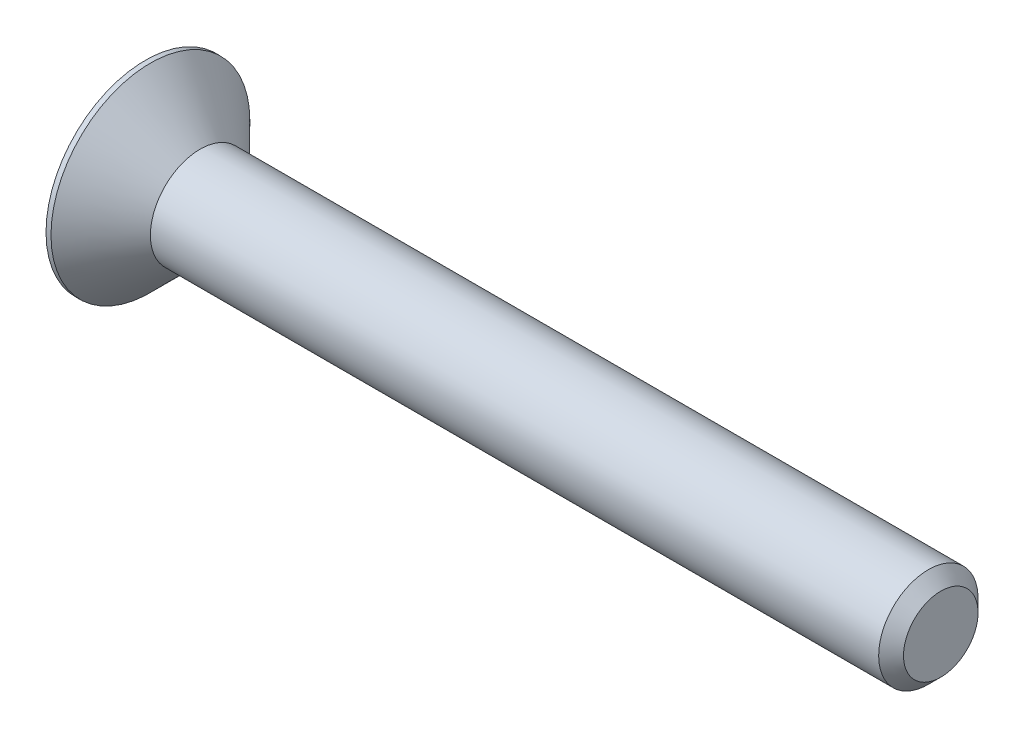
SolidWorks part; units mm, degrees
ref_plane "Front Plane" through (0, 0, 0) normal (0, 0, 1) x (1, 0, 0)
ref_plane "Top Plane" through (0, 0, 0) normal (0, 1, 0) x (1, 0, 0)
ref_plane "Right Plane" through (0, 0, 0) normal (1, 0, 0) x (0, 0, -1)
sketch "Sketch2" plane through (0, 0, 0) normal (0, 0, 1) x (1, 0, 0)
  line L0 (0, 0) -> (0, 2)
  line L1 (0, 2) -> (0.1, 2)
  line L2 (0.1, 2) -> (1.1, 1)
  line L3 (1.1, 1) -> (15.75, 1)
  line L4 (15.75, 1) -> (16, 0.75)
  line L5 (16, 0.75) -> (16, 0)
  line L6 (16, 0) -> (0, 0)
  line L7 (-2.2818, 0) -> (8.0811, 0) construction
  dimension "D1" = 4
  dimension "D2" = 0.1
  dimension "D3" = 45
  dimension "D4" = 16
  dimension "D5" = 0.25
  dimension "D6" = 2
revolve "Revolve1" add sketch "Sketch2" angle 360 about L7
sketch "Sketch3" plane through (0, 0, 0) normal (-1, 0, 0) x (0, 0, 1)
  line L1 (0.433, -0.75) -> (0.866, 0)
  line L2 (0.866, 0) -> (0.433, 0.75)
  line L3 (0.433, 0.75) -> (-0.433, 0.75)
  line L4 (-0.433, 0.75) -> (-0.866, 0)
  line L5 (-0.866, 0) -> (-0.433, -0.75)
  line L6 (-0.433, -0.75) -> (0.433, -0.75)
  circle A0 centre (0, 0) radius 0.75 construction
  dimension "D1" = 1.5
extrude "Cut-Extrude1" cut sketch "Sketch3" against normal blind 0.8
